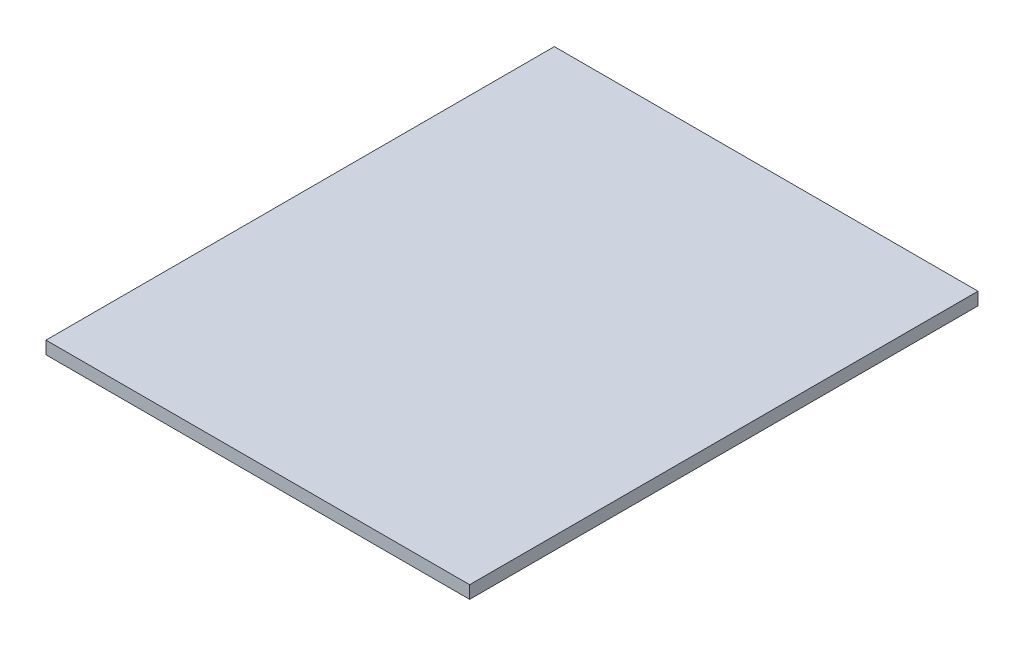
SolidWorks part; units mm, degrees
material "Cedar"
ref_plane "Front" through (0, 0, 0) normal (0, 0, 1) x (1, 0, 0)
ref_plane "Top" through (0, 0, 0) normal (0, 1, 0) x (1, 0, 0)
ref_plane "Right" through (0, 0, 0) normal (1, 0, 0) x (0, 0, -1)
sketch "Sketch1" plane through (0, 0, 0) normal (0, 1, 0) x (1, 0, 0)
  line L1 (-190.5, 228.6) -> (190.5, 228.6)
  line L2 (-190.5, 228.6) -> (-190.5, -228.6)
  line L3 (-190.5, -228.6) -> (190.5, -228.6)
  line L4 (190.5, 228.6) -> (190.5, -228.6)
  line L5 (-190.5, 228.6) -> (190.5, -228.6) construction
  line L6 (-190.5, -228.6) -> (190.5, 228.6) construction
  point P0 (0, 0)
  dimension "D1" = 457.2
  dimension "D2" = 381
extrude "Boss-Extrude1" add sketch "Sketch1" along normal blind 11.4554 contours L1 L4 L3 L2
